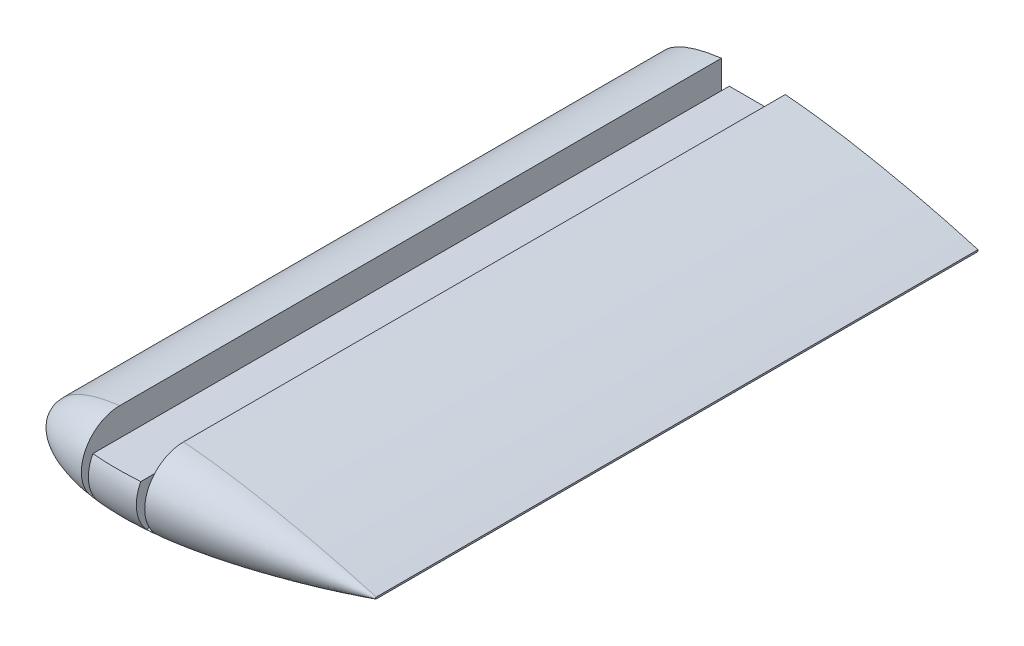
SolidWorks part; units mm, degrees
ref_plane "Спереди" through (0, 0, 0) normal (0, 0, 1) x (1, 0, 0)
ref_plane "Сверху" through (0, 0, 0) normal (0, 1, 0) x (1, 0, 0)
ref_plane "Справа" through (0, 0, 0) normal (1, 0, 0) x (0, 0, -1)
other "Configuration Table"
curve "Curve1"
  spline degree 3 poles (1, 0.0026, 0) (0.9995, 0.0028, 0) (0.9974, 0.0034, 0) (0.9928, 0.0047, 0) (0.9852, 0.0069, 0) (0.9746, 0.01, 0) (0.961, 0.0138, 0) (0.9446, 0.0183, 0) (0.9255, 0.0235, 0) (0.9037, 0.0292, 0) (0.8794, 0.0355, 0) (0.8529, 0.0421, 0) (0.8241, 0.0491, 0) (0.7933, 0.0562, 0) (0.7607, 0.0635, 0) (0.7266, 0.0709, 0) (0.691, 0.0782, 0) (0.6542, 0.0854, 0) (0.6165, 0.0923, 0) (0.5781, 0.0988, 0) (0.5392, 0.1049, 0) (0.5, 0.1104, 0) (0.4609, 0.1152, 0) (0.422, 0.1192, 0) (0.3836, 0.1222, 0) (0.3458, 0.1243, 0) (0.3091, 0.1252, 0) (0.2735, 0.1249, 0) (0.2392, 0.1234, 0) (0.2066, 0.1205, 0) (0.1758, 0.1164, 0) (0.147, 0.111, 0) (0.1203, 0.1043, 0) (0.096, 0.0965, 0) (0.0741, 0.0875, 0) (0.0549, 0.0774, 0) (0.0383, 0.0665, 0) (0.0245, 0.0546, 0) (0.0137, 0.042, 0) (0.0058, 0.0286, 0) (0.001, 0.0145, 0) (-0.0005, 0, 0) (0.001, -0.0145, 0) (0.0058, -0.0286, 0) (0.0137, -0.042, 0) (0.0245, -0.0546, 0) (0.0383, -0.0665, 0) (0.0549, -0.0774, 0) (0.0741, -0.0875, 0) (0.096, -0.0965, 0) (0.1203, -0.1043, 0) (0.147, -0.111, 0) (0.1758, -0.1164, 0) (0.2066, -0.1205, 0) (0.2392, -0.1234, 0) (0.2735, -0.1249, 0) (0.3091, -0.1252, 0) (0.3458, -0.1243, 0) (0.3836, -0.1222, 0) (0.422, -0.1192, 0) (0.4609, -0.1152, 0) (0.5, -0.1104, 0) (0.5392, -0.1049, 0) (0.5781, -0.0988, 0) (0.6165, -0.0923, 0) (0.6542, -0.0854, 0) (0.691, -0.0782, 0) (0.7266, -0.0709, 0) (0.7607, -0.0635, 0) (0.7933, -0.0562, 0) (0.8241, -0.0491, 0) (0.8529, -0.0421, 0) (0.8794, -0.0355, 0) (0.9037, -0.0292, 0) (0.9255, -0.0235, 0) (0.9446, -0.0183, 0) (0.961, -0.0138, 0) (0.9746, -0.01, 0) (0.9852, -0.0069, 0) (0.9928, -0.0047, 0) (0.9974, -0.0034, 0) (0.9995, -0.0028, 0) (1, -0.0026, 0) knots 0 0 0 0 0.000754 0.003013 0.006759 0.011967 0.018601 0.026614 0.035953 0.046555 0.058348 0.071256 0.085193 0.100071 0.115793 0.132259 0.149363 0.166997 0.185048 0.203403 0.221946 0.240561 0.259134 0.27755 0.295701 0.313483 0.330797 0.347552 0.363666 0.379065 0.393686 0.407475 0.420392 0.432406 0.443503 0.453686 0.462984 0.471456 0.479204 0.486388 0.493229 0.5 0.506771 0.513612 0.520796 0.528544 0.537016 0.546314 0.556497 0.567594 0.579608 0.592525 0.606314 0.620935 0.636334 0.652448 0.669203 0.686517 0.704299 0.72245 0.740866 0.759439 0.778054 0.796597 0.814952 0.833003 0.850637 0.867741 0.884207 0.899929 0.914807 0.928744 0.941652 0.953445 0.964047 0.973386 0.981399 0.988033 0.993241 0.996987 0.999246 1 1 1 1
sketch "Sketch2" plane through (0, 0, 0) normal (0, 0, 1) x (1, 0, 0)
  line L0 (55.999, 0.2099) -> (55.999, -0.2099) construction
  line L1 (55.999, 0) -> (-23.9777, 0) construction
  line L2 (-23.9777, 0) -> (-23.9777, 20.1567) construction
  line L3 (-7.5754, 10) -> (21.8908, 10) construction
  line L4 (55.999, 0.2099) -> (55.999, -0.2099)
  line L5 (0, 10) -> (0, -10) construction
  line L6 (55.999, -0.2099) -> (55.999, 14.9208) construction
  spline S1 degree 3 poles (55.999, 0.2099) (53.4639, 0.9505) (48.8039, 2.2339) (42.4289, 3.8199) (36.7434, 5.1209) (31.1997, 6.2872) (25.2824, 7.4075) (20.1765, 8.2452) (14.9796, 8.9749) (10.8215, 9.4486) (6.6974, 9.777) (3.6807, 9.9396) (0.7396, 10.0127) (-2.1078, 9.99) (-4.8439, 9.867) (-7.4522, 9.6409) (-9.9165, 9.3106) (-12.2218, 8.8772) (-14.354, 8.3437) (-16.3004, 7.7143) (-18.0494, 6.9954) (-19.5906, 6.1934) (-20.9154, 5.3156) (-22.0159, 4.3681) (-22.8849, 3.3565) (-23.5145, 2.285) (-23.8954, 1.1588) (-24.0187, 0) (-23.8954, -1.1588) (-23.5145, -2.285) (-22.8849, -3.3565) (-22.0159, -4.3681) (-20.9154, -5.3156) (-19.5906, -6.1934) (-18.0494, -6.9954) (-16.3004, -7.7143) (-14.354, -8.3437) (-12.2218, -8.8772) (-9.9165, -9.3106) (-7.4522, -9.6409) (-4.8439, -9.867) (-2.1078, -9.99) (0.7396, -10.0127) (3.6807, -9.9396) (7.7407, -9.7208) (12.9128, -9.2413) (19.1367, -8.4158) (25.2824, -7.4074) (31.1998, -6.2873) (37.5172, -4.9581) (44.7426, -3.2759) (51.0576, -1.6263) (54.945, -0.5178) (55.9579, -0.2219) (55.999, -0.2099) knots 0 0 0 0 0.046555 0.085193 0.115793 0.149363 0.185048 0.221946 0.240561 0.27755 0.295701 0.313483 0.330797 0.347552 0.363666 0.379065 0.393686 0.407475 0.420392 0.432406 0.443503 0.453686 0.462984 0.471456 0.479204 0.486388 0.493229 0.5 0.506771 0.513612 0.520796 0.528544 0.537016 0.546314 0.556497 0.567594 0.579608 0.592525 0.606314 0.620935 0.636334 0.652448 0.669203 0.686517 0.704299 0.740866 0.778054 0.814952 0.850637 0.884207 0.928744 0.981399 0.999246 1 1 1 1
  point P11 (0, 0)
  dimension "D1" = 20
extrude "Boss-Extrude1" add sketch "Sketch2" along normal blind 150
sketch "Sketch4" plane through (0, 0, 150) normal (0, 0, 1) x (1, 0, 0)
  line L0 (55.999, 0) -> (-23.9777, 0)
  line L1 (55.999, -0.2099) -> (55.999, 0.2099) construction
  line L3 (55.999, -0.2099) -> (55.999, 0.2099)
  line L4 (55.999, 0) -> (55.999, 0.2099)
  spline S0 degree 3 poles (55.999, 0.2099) (53.4639, 0.9505) (48.8039, 2.2339) (42.4289, 3.8199) (36.7434, 5.1209) (31.1997, 6.2872) (25.2824, 7.4075) (20.1765, 8.2452) (14.9796, 8.9749) (10.8215, 9.4486) (6.6974, 9.777) (3.6807, 9.9396) (0.7396, 10.0127) (-2.1078, 9.99) (-4.8439, 9.867) (-7.4522, 9.6409) (-9.9165, 9.3106) (-12.2218, 8.8772) (-14.354, 8.3437) (-16.3004, 7.7143) (-18.0494, 6.9954) (-19.5906, 6.1934) (-20.9154, 5.3156) (-22.0159, 4.3681) (-22.8849, 3.3565) (-23.5145, 2.285) (-23.8954, 1.1588) (-24.0187, 0) (-23.8954, -1.1588) (-23.5145, -2.285) (-22.8849, -3.3565) (-22.0159, -4.3681) (-20.9154, -5.3156) (-19.5906, -6.1934) (-18.0494, -6.9954) (-16.3004, -7.7143) (-14.354, -8.3437) (-12.2218, -8.8772) (-9.9165, -9.3106) (-7.4522, -9.6409) (-4.8439, -9.867) (-2.1078, -9.99) (0.7396, -10.0127) (3.6807, -9.9396) (7.7407, -9.7208) (12.9128, -9.2413) (19.1367, -8.4158) (25.2824, -7.4074) (31.1998, -6.2873) (37.5172, -4.9581) (44.7426, -3.2759) (51.0576, -1.6263) (54.945, -0.5178) (55.9579, -0.2219) (55.999, -0.2099) knots 0 0 0 0 0.046555 0.085193 0.115793 0.149363 0.185048 0.221946 0.240561 0.27755 0.295701 0.313483 0.330797 0.347552 0.363666 0.379065 0.393686 0.407475 0.420392 0.432406 0.443503 0.453686 0.462984 0.471456 0.479204 0.486388 0.493229 0.5 0.506771 0.513612 0.520796 0.528544 0.537016 0.546314 0.556497 0.567594 0.579608 0.592525 0.606314 0.620935 0.636334 0.652448 0.669203 0.686517 0.704299 0.740866 0.778054 0.814952 0.850637 0.884207 0.928744 0.981399 0.999246 1 1 1 1 construction
  spline S2 degree 3 poles (-635.3554, -2880.1705) (392.2047, -313.7808) (246.3383, -46.9116) (42.4289, 3.8199) (36.7434, 5.1209) (31.1997, 6.2872) (25.2824, 7.4075) (20.1765, 8.2452) (14.9796, 8.9749) (10.8215, 9.4486) (6.6974, 9.777) (3.6807, 9.9396) (0.7396, 10.0127) (-2.1078, 9.99) (-4.8439, 9.867) (-7.4522, 9.6409) (-9.9165, 9.3106) (-12.2218, 8.8772) (-14.354, 8.3437) (-16.3004, 7.7143) (-18.0494, 6.9954) (-19.5906, 6.1934) (-20.9154, 5.3156) (-22.0159, 4.3681) (-22.8849, 3.3565) (-23.5145, 2.285) (-23.8954, 1.1588) (-24.0187, 0) (-23.8954, -1.1588) (-23.5145, -2.285) (-22.8849, -3.3565) (-22.0159, -4.3681) (-20.9154, -5.3156) (-19.5906, -6.1934) (-18.0494, -6.9954) (-16.3004, -7.7143) (-14.354, -8.3437) (-12.2218, -8.8772) (-9.9165, -9.3106) (-7.4522, -9.6409) (-4.8439, -9.867) (-2.1078, -9.99) (0.7396, -10.0127) (3.6807, -9.9396) (7.7407, -9.7208) (12.9128, -9.2413) (19.1367, -8.4158) (25.2824, -7.4074) (31.1998, -6.2873) (37.5172, -4.9581) (44.7426, -3.2759) (51.0576, -1.6263) (81.4934, 7.0521) (107.6521, 19.7196) (975.9197, -2854.3918) knots -3.587955 -3.587955 -3.587955 -3.587955 0.046555 0.085193 0.115793 0.149363 0.185048 0.221946 0.240561 0.27755 0.295701 0.313483 0.330797 0.347552 0.363666 0.379065 0.393686 0.407475 0.420392 0.432406 0.443503 0.453686 0.462984 0.471456 0.479204 0.486388 0.493229 0.5 0.506771 0.513612 0.520796 0.528544 0.537016 0.546314 0.556497 0.567594 0.579608 0.592525 0.606314 0.620935 0.636334 0.652448 0.669203 0.686517 0.704299 0.740866 0.778054 0.814952 0.850637 0.884207 0.928744 0.981399 0.999246 1.486622 1.486622 1.486622 1.486622 only from (55.999, 0.2099) to (55.999, -0.2099)
  spline S3 degree 3 poles (55.999, 0.2099) (53.4639, 0.9505) (48.8039, 2.2339) (42.4289, 3.8199) (36.7434, 5.1209) (31.1997, 6.2872) (25.2824, 7.4075) (20.1765, 8.2452) (14.9796, 8.9749) (10.8215, 9.4486) (6.6974, 9.777) (3.6807, 9.9396) (0.7396, 10.0127) (-2.1078, 9.99) (-4.8439, 9.867) (-7.4522, 9.6409) (-9.9165, 9.3106) (-12.2218, 8.8772) (-14.354, 8.3437) (-16.3004, 7.7143) (-18.0494, 6.9954) (-19.5906, 6.1934) (-20.9154, 5.3156) (-22.0159, 4.3681) (-22.8849, 3.3565) (-23.5145, 2.285) (-23.8954, 1.1588) (-23.9777, 0.3849) (-23.9777, 0) knots 0 0 0 0 0.046555 0.085193 0.115793 0.149363 0.185048 0.221946 0.240561 0.27755 0.295701 0.313483 0.330797 0.347552 0.363666 0.379065 0.393686 0.407475 0.420392 0.432406 0.443503 0.453686 0.462984 0.471456 0.479204 0.486388 0.493229 0.5 0.5 0.5 0.5
  dimension "D1" = 0
revolve "Revolve1" add sketch "Sketch4" angle 180 about L0
sketch "Sketch3" plane through (0, 0, 0) normal (0, 0, -1) x (-1, 0, 0)
  line L0 (6, -6.5) -> (7.95, -6.5)
  line L2 (-6, -6.5) -> (-6, 4.5)
  line L3 (-6, 4.5) -> (6, 4.5)
  line L4 (6, -6.5) -> (6, 4.5)
  line L5 (-6, -6.5) -> (6, 4.5) construction
  line L6 (-6, 4.5) -> (6, -6.5) construction
  line L7 (7.95, -6.5) -> (7.95, 9.5637)
  line L8 (-6, -6.5) -> (-7.95, -6.5)
  line L9 (-7.95, -6.5) -> (-7.95, 9.6738)
  line L10 (-11.2468, 10) -> (11.5184, 10) construction
  line L11 (0, 0) -> (0, 6.0357) construction
  line L12 (-7.95, -6.5) -> (7.95, -6.5) construction
  spline S0 degree 3 poles (275.2851, -1947.3186) (-351.5026, -245.2226) (-218.8463, -40.0718) (-42.4289, 3.8199) (-36.7434, 5.1209) (-31.1997, 6.2872) (-25.2824, 7.4075) (-20.1765, 8.2452) (-14.9796, 8.9749) (-10.8215, 9.4486) (-6.6974, 9.777) (-3.6807, 9.9396) (-0.7396, 10.0127) (2.1078, 9.99) (4.8439, 9.867) (7.4522, 9.6409) (9.9165, 9.3106) (12.2218, 8.8772) (14.354, 8.3437) (16.3004, 7.7143) (18.0494, 6.9954) (19.5906, 6.1934) (20.9154, 5.3156) (22.0159, 4.3681) (22.8849, 3.3565) (23.5145, 2.285) (23.8954, 1.1588) (24.0187, 0) (23.8954, -1.1588) (23.5145, -2.285) (22.8849, -3.3565) (22.0159, -4.3681) (20.9154, -5.3156) (19.5906, -6.1934) (18.0494, -6.9954) (16.3004, -7.7143) (14.354, -8.3437) (12.2218, -8.8772) (9.9165, -9.3106) (7.4522, -9.6409) (4.8439, -9.867) (2.1078, -9.99) (-0.7396, -10.0127) (-3.6807, -9.9396) (-7.7407, -9.7208) (-12.9128, -9.2413) (-19.1367, -8.4158) (-25.2824, -7.4074) (-31.1998, -6.2873) (-37.5172, -4.9581) (-44.7426, -3.2759) (-51.0576, -1.6263) (-78.1348, 6.0944) (-101.2564, 16.704) (-685.5525, -1897.6172) knots -3.088599 -3.088599 -3.088599 -3.088599 0.046555 0.085193 0.115793 0.149363 0.185048 0.221946 0.240561 0.27755 0.295701 0.313483 0.330797 0.347552 0.363666 0.379065 0.393686 0.407475 0.420392 0.432406 0.443503 0.453686 0.462984 0.471456 0.479204 0.486388 0.493229 0.5 0.506771 0.513612 0.520796 0.528544 0.537016 0.546314 0.556497 0.567594 0.579608 0.592525 0.606314 0.620935 0.636334 0.652448 0.669203 0.686517 0.704299 0.740866 0.778054 0.814952 0.850637 0.884207 0.928744 0.981399 0.999246 1.425061 1.425061 1.425061 1.425061 only from (-55.999, 0.2099) to (-55.999, -0.2099) construction
  spline S1 degree 3 poles (-7.95, 9.6738) (-7.5253, 9.7065) (-6.0943, 9.8095) (-3.6807, 9.9396) (-0.7396, 10.0127) (2.1078, 9.99) (4.8439, 9.867) (6.7781, 9.6993) (7.7981, 9.5819) (7.95, 9.5637) knots 0.288193 0.288193 0.288193 0.288193 0.295701 0.313483 0.330797 0.347552 0.363666 0.379065 0.381762 0.381762 0.381762 0.381762
  point P0 (0, -1)
  point P13 (-6.975, -6.5)
  dimension "D1" = 12
  dimension "D2" = 11
  dimension "D3" = 1.95
  dimension "D4" = 1.95
  dimension "D5" = 16.5
extrude "Cut-Extrude1" cut sketch "Sketch3" against normal up to next
